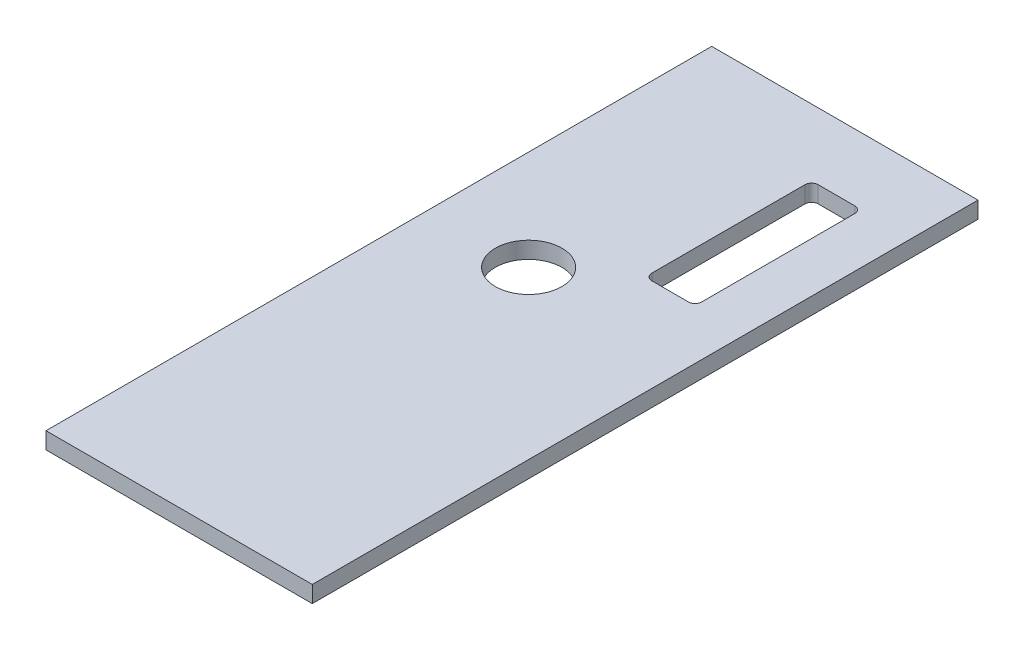
SolidWorks part; units mm, degrees
ref_plane "Front Plane" through (0, 0, 0) normal (0, 0, 1) x (1, 0, 0)
ref_plane "Top Plane" through (0, 0, 0) normal (0, 1, 0) x (1, 0, 0)
ref_plane "Right Plane" through (0, 0, 0) normal (1, 0, 0) x (0, 0, -1)
sketch "Sketch1" plane through (0, 0, 0) normal (0, 1, 0) x (1, 0, 0)
  line L1 (50.8, -127) -> (-50.8, -127)
  line L2 (50.8, -127) -> (50.8, 127)
  line L3 (50.8, 127) -> (-50.8, 127)
  line L4 (-50.8, -127) -> (-50.8, 127)
  line L5 (50.8, -127) -> (-50.8, 127) construction
  line L6 (50.8, 127) -> (-50.8, -127) construction
  line L7 (29.21, 101.6) -> (15.24, 101.6)
  line L8 (31.75, 99.06) -> (31.75, 40.64)
  line L9 (29.21, 38.1) -> (15.24, 38.1)
  line L10 (12.7, 99.06) -> (12.7, 40.64)
  circle A0 centre (-12.7, 19.05) radius 12.7
  arc A1 (15.24, 38.1) -> (12.7, 40.64) centre (15.24, 40.64) cw
  arc A2 (31.75, 40.64) -> (29.21, 38.1) centre (29.21, 40.64) cw
  arc A3 (29.21, 101.6) -> (31.75, 99.06) centre (29.21, 99.06) cw
  arc A4 (15.24, 101.6) -> (12.7, 99.06) centre (15.24, 99.06) ccw
  point P0 (0, 0)
  point P12 (-25.4, 19.05)
  point P13 (-12.7, 31.75)
  point P16 (12.7, 38.1)
  point P19 (31.75, 38.1)
  point P22 (31.75, 101.6)
  dimension "D2" = 25.4
  dimension "D10" = 2.54
  dimension "D1" = 101.6
  dimension "D3" = 19.05
  dimension "D4" = 19.05
  dimension "D5" = 63.5
  dimension "D6" = 25.4
  dimension "D7" = 95.25
  dimension "D8" = 25.4
  dimension "D9" = 254
extrude "Boss-Extrude1" add sketch "Sketch1" along normal blind 6.35 contours L4 L3 L2 L1
